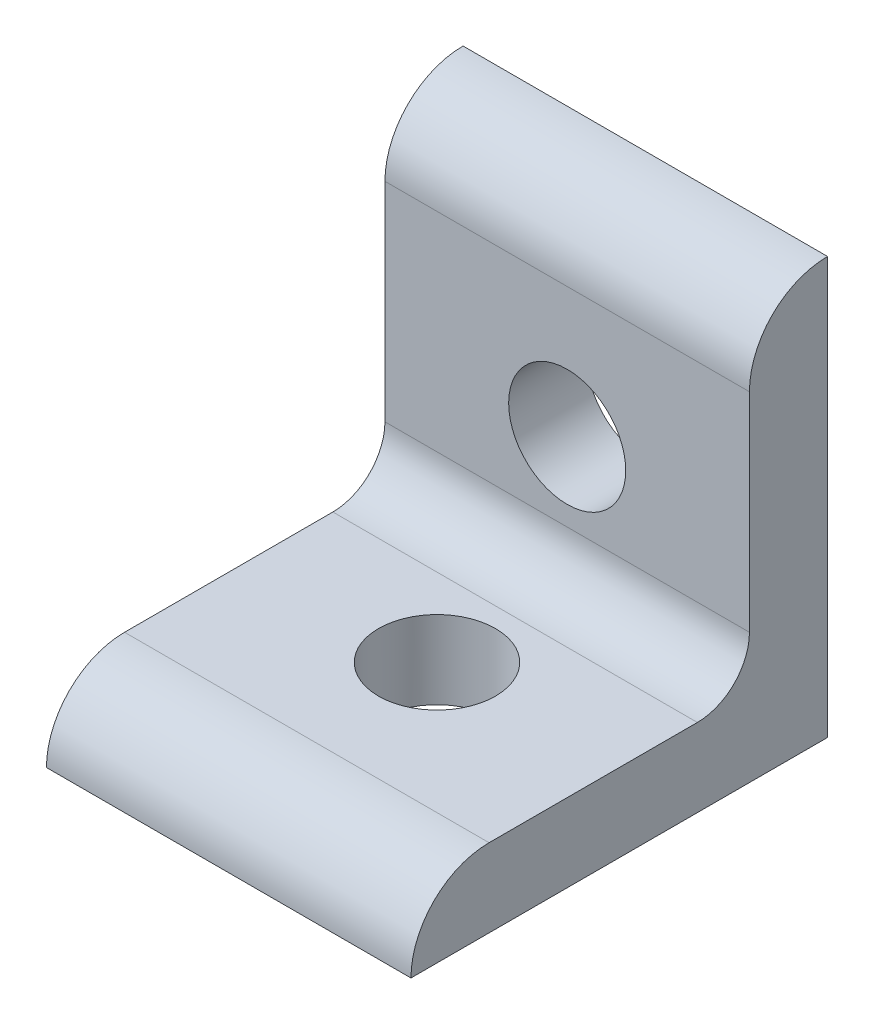
SolidWorks part; units mm, degrees
material "6105-T5 Aluminum"
ref_plane "Front Plane" through (0, 0, 0) normal (0, 0, 1) x (1, 0, 0)
ref_plane "Top Plane" through (0, 0, 0) normal (0, 1, 0) x (1, 0, 0)
ref_plane "Right Plane" through (0, 0, 0) normal (1, 0, 0) x (0, 0, -1)
ref_plane "Plane1" through (0, -22.225, 0) normal (0, -1, 0) x (1, 0, 0)
sketch "Sketch1" plane through (0, -22.225, 0) normal (-1, 0, 0) x (0, -1, 0)
  line L0 (0, 0) -> (0, 25.4)
  line L1 (-4.7625, 20.6375) -> (-4.7625, 7.9375)
  line L2 (-7.9375, 4.7625) -> (-20.6375, 4.7625)
  line L3 (-25.4, 0) -> (0, 0)
  arc A0 (0, 25.4) -> (-4.7625, 20.6375) centre (0, 20.6375) ccw
  arc A1 (-20.6375, 4.7625) -> (-25.4, 0) centre (-20.6375, 0) ccw
  arc A2 (-7.9375, 4.7625) -> (-4.7625, 7.9375) centre (-7.9375, 7.9375) ccw
  dimension "D1" = 3.175
extrude "Boss-Extrude1" add sketch "Sketch1" against normal mid plane 22.225
sketch "Sketch6" plane through (0, -22.225, 0) normal (0, -1, 0) x (-1, 0, 0)
  circle A0 centre (0, -12.7) radius 3.5687
  dimension "D1" = 7.1374
extrude "Cut-Extrude1" cut sketch "Sketch6" against normal blind 7.62
sketch "Sketch7" plane through (0, 0, 0) normal (0, 0, -1) x (-1, 0, 0)
  circle A0 centre (0, -9.525) radius 3.5687
  dimension "D1" = 7.1374
extrude "Cut-Extrude2" cut sketch "Sketch7" against normal blind 7.62
